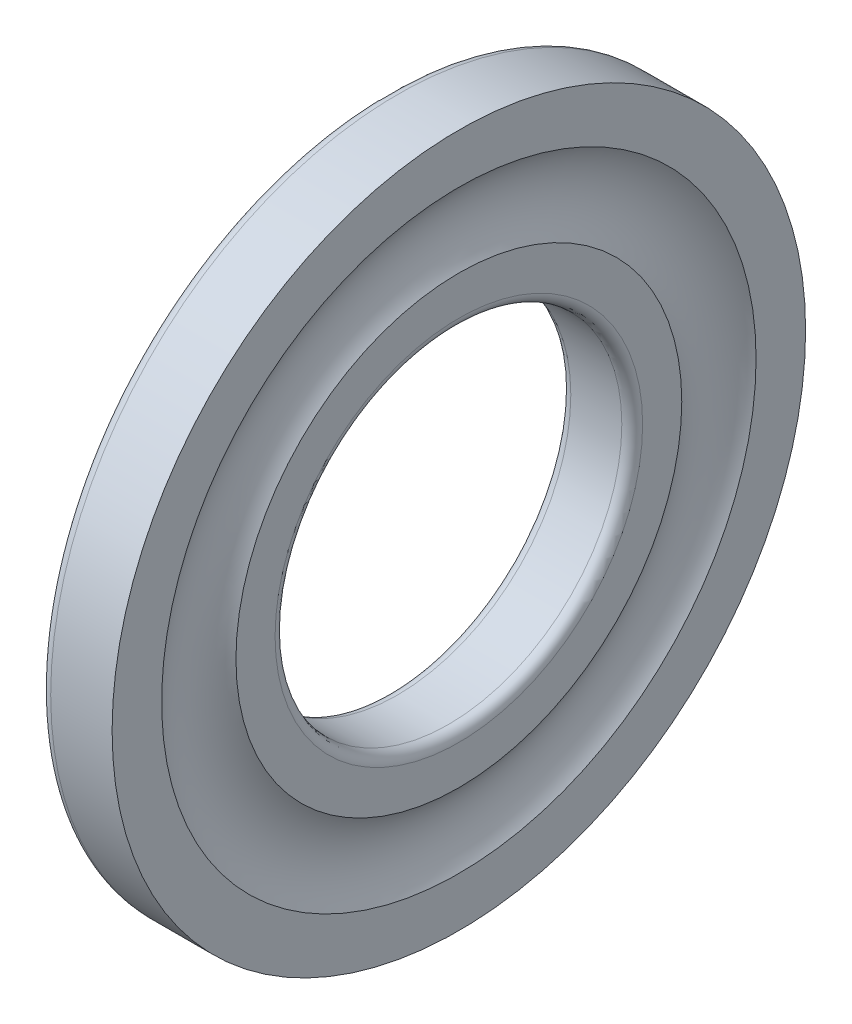
SolidWorks part; units mm, degrees
ref_plane "Alzado" through (0, 0, 0) normal (0, 0, 1) x (1, 0, 0)
ref_plane "Planta" through (0, 0, 0) normal (0, 1, 0) x (1, 0, 0)
ref_plane "Vista lateral" through (0, 0, 0) normal (1, 0, 0) x (0, 0, -1)
ref_plane "Plano1" through (0, 0, 0) normal (0, 0, 1) x (1, 0, 0)
sketch "Croquis1" plane through (0, 0, 0) normal (0, 0, 1) x (1, 0, 0)
  line L0 (0.6, 10) -> (3.542, 10)
  line L1 (4.142, 10.6) -> (4.142, 12.8573)
  line L2 (4.142, 17.1427) -> (4.142, 20)
  line L3 (4.142, 20) -> (0.6, 20)
  line L4 (0, 19.4) -> (0, 10.6)
  line L5 (3.542, 0) -> (0.6, 0) construction
  arc A0 (0, 10.6) -> (0.6, 10) centre (0.6, 10.6) ccw
  arc A1 (3.542, 10) -> (4.142, 10.6) centre (3.542, 10.6) ccw
  arc A2 (4.142, 12.8573) -> (4.142, 17.1427) centre (7, 15) cw
  arc A3 (0.6, 20) -> (0, 19.4) centre (0.6, 19.4) ccw
revolve "Revolución1" add sketch "Croquis1" angle 360 about L5
